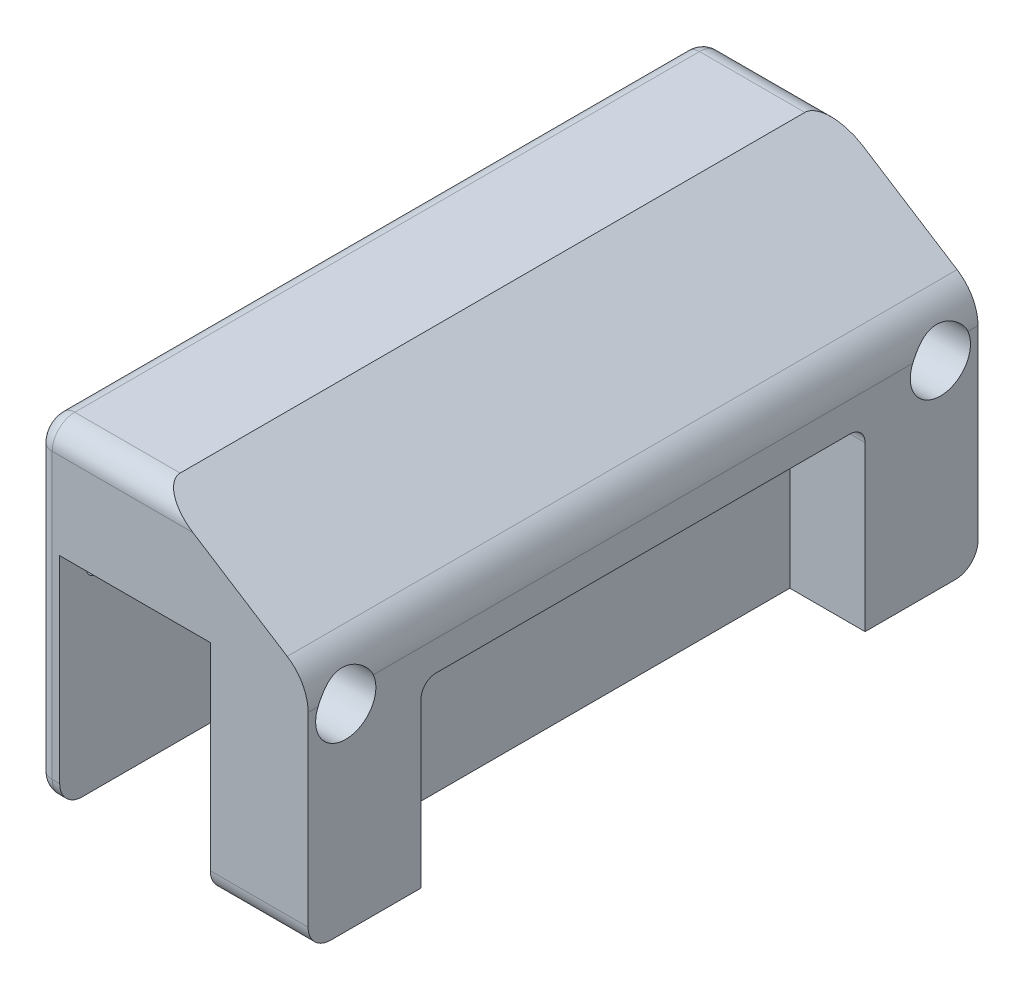
SolidWorks part; units mm, degrees
material "ABS"
ref_plane "Plano frontal" through (0, 0, 0) normal (0, 0, 1) x (1, 0, 0)
ref_plane "Plano superior" through (0, 0, 0) normal (0, 1, 0) x (1, 0, 0)
ref_plane "Plano direito" through (0, 0, 0) normal (1, 0, 0) x (0, 0, -1)
sketch "Esboço2" plane through (0, 0, 0) normal (1, 0, 0) x (0, 0, -1)
  line L1 (2.9016, -0.0625) -> (-35.0984, -0.0625) construction
  line L2 (2.9016, -0.0625) -> (-35.0984, -0.0625)
  line L6 (7.6893, -0.0625) -> (2.9016, -0.0625)
  line L8 (-39.8861, -0.0625) -> (-35.0984, -0.0625)
  line L9 (-60.5984, 9.4769) -> (-60.5984, 20.9769)
  line L10 (28.4016, 9.4769) -> (28.4016, 20.9769)
  line L11 (-57.5984, 23.9769) -> (25.4016, 23.9769)
  arc A0 (28.4016, 20.9769) -> (25.4016, 23.9769) centre (25.4016, 20.9769) ccw
  arc A1 (-60.5984, 20.9769) -> (-57.5984, 23.9769) centre (-57.5984, 20.9769) cw
  arc A2 (28.4016, 9.4769) -> (24.5016, 12.3387) centre (25.4016, 9.4769) ccw
  arc A3 (-48.8914, 5.5897) -> (-56.6984, 12.3387) centre (-60.5984, -0.0625) ccw
  arc A4 (-48.8914, 5.5897) -> (-39.8861, -0.0625) centre (-39.8861, 9.9375) ccw
  arc A5 (-60.5984, 9.4769) -> (-56.6984, 12.3387) centre (-57.5984, 9.4769) cw
  arc A6 (16.6946, 5.5897) -> (7.6893, -0.0625) centre (7.6893, 9.9375) cw
  arc A7 (16.6946, 5.5897) -> (24.5016, 12.3387) centre (28.4016, -0.0625) cw
  point P22 (28.4016, 12.9375)
  point P23 (-60.5984, 12.9375)
  dimension "D1" = 3
extrude "Ressalto-extrusão2" add sketch "Esboço2" along normal blind 30
sketch "Esboço3" plane through (0, 0, 0) normal (-1, 0, 0) x (0, 0, 1)
  line L0 (60.5984, 15.2269) -> (60.5984, 20.9769)
  line L1 (60.5984, 20.9769) -> (60.5984, 9.4769) construction
  line L2 (-28.4016, 15.2269) -> (-28.4016, 20.9769)
  line L3 (-28.4016, 9.4769) -> (-28.4016, 20.9769) construction
  line L4 (16.0984, 23.9769) -> (57.5984, 23.9769)
  line L5 (-25.4016, 23.9769) -> (57.5984, 23.9769) construction
  line L6 (16.0984, 23.9769) -> (-25.4016, 23.9769)
  line L7 (60.5984, 15.2269) -> (60.5984, -16.7731)
  line L8 (-28.4016, 15.2269) -> (-28.4016, -16.7731)
  line L9 (57.5984, -19.7731) -> (-25.4016, -19.7731)
  arc A0 (57.5984, 23.9769) -> (60.5984, 20.9769) centre (57.5984, 20.9769) cw
  arc A1 (-28.4016, 20.9769) -> (-25.4016, 23.9769) centre (-25.4016, 20.9769) cw
  arc A2 (-28.4016, -16.7731) -> (-25.4016, -19.7731) centre (-25.4016, -16.7731) ccw
  arc A3 (60.5984, -16.7731) -> (57.5984, -19.7731) centre (57.5984, -16.7731) cw
  dimension "D1" = 3
  dimension "D2" = 3
extrude "Ressalto-extrusão3" add sketch "Esboço3" along normal blind 3
sketch "Esboço4" plane through (30, 0, 0) normal (1, 0, 0) x (0, 0, -1)
  line L0 (-16.0984, 23.9769) -> (25.4016, 23.9769)
  line L1 (25.4016, 23.9769) -> (-57.5984, 23.9769) construction
  line L2 (-16.0984, 23.9769) -> (-57.5984, 23.9769)
  line L3 (28.4016, 15.2269) -> (28.4016, 20.9769)
  line L4 (28.4016, 9.4769) -> (28.4016, 20.9769) construction
  line L5 (-60.5984, 20.9769) -> (-60.5984, 15.2269)
  line L7 (28.4016, 15.2269) -> (28.4016, -16.7731)
  line L8 (28.4016, 9.4769) -> (28.4016, -16.7731) construction
  line L9 (-60.5984, 20.9769) -> (-60.5984, 9.4769) construction
  line L10 (-60.5984, 15.2269) -> (-60.5984, -16.7731)
  line L11 (25.4016, -19.7731) -> (-57.5984, -19.7731)
  arc A0 (25.4016, 23.9769) -> (28.4016, 20.9769) centre (25.4016, 20.9769) cw
  arc A1 (-60.5984, 20.9769) -> (-57.5984, 23.9769) centre (-57.5984, 20.9769) cw
  arc A2 (-60.5984, -16.7731) -> (-57.5984, -19.7731) centre (-57.5984, -16.7731) ccw
  arc A3 (28.4016, -16.7731) -> (25.4016, -19.7731) centre (25.4016, -16.7731) cw
  point P23 (28.4016, -19.7731)
  dimension "D1" = 3
extrude "Ressalto-extrusão4" add sketch "Esboço4" along normal blind 3 and the other way blind 10
sketch "Esboço8" plane through (33, 0, 0) normal (1, 0, 0) x (0, 0, -1)
  line L0 (-60.5984, 20.9769) -> (-60.5984, -16.7731) construction
  line L1 (-43.5984, 3.9769) -> (11.4016, 3.9769)
  line L2 (-45.5984, 1.9769) -> (-45.5984, -7.7731)
  line L4 (13.4016, 1.9769) -> (13.4016, -7.7731)
  line L5 (28.4016, -16.7731) -> (28.4016, 20.9769) construction
  line L6 (25.4016, 23.9769) -> (-57.5984, 23.9769) construction
  line L7 (-57.5984, -19.7731) -> (25.4016, -19.7731) construction
  line L9 (-45.5984, -7.7731) -> (-45.5984, -19.7731)
  line L10 (-45.5984, -19.7731) -> (13.4016, -19.7731)
  line L11 (13.4016, -7.7731) -> (13.4016, -19.7731)
  arc A0 (-43.5984, 3.9769) -> (-45.5984, 1.9769) centre (-43.5984, 1.9769) ccw
  arc A2 (11.4016, 3.9769) -> (13.4016, 1.9769) centre (11.4016, 1.9769) cw
  point P1 (0, 0)
  point P2 (0, 0)
  point P10 (0, 0)
  point P11 (13.4016, -19.7731)
  point P12 (-45.5984, -19.7731)
  point P13 (0, 0)
  point P19 (13.8268, -19.7731)
  point P22 (13.4016, 3.9769)
  point P23 (-45.5984, -19.4909)
  point P28 (13.4016, -9.7731)
  point P31 (13.4016, -19.7731)
  dimension "D9" = 2
  dimension "D10" = 0
  dimension "D1" = 15
  dimension "D2" = 15
  dimension "D3" = 20
  dimension "D4" = 0
  dimension "D5" = 15
  dimension "D6" = 15
  dimension "D7" = 0
  dimension "D8" = 10
extrude "Corte-extrusão1" cut sketch "Esboço8" against normal blind 10
sketch "Esboço9" plane through (0, -19.7731, 0) normal (0, -1, 0) x (-1, 0, 0)
  line L0 (-20, 28.4016) -> (-33, 28.4016) construction
  line L1 (-25, 13.4016) -> (-28, 13.4016)
  line L2 (-23, 11.4016) -> (-23, -43.5984)
  line L3 (-25, -45.5984) -> (-28, -45.5984)
  line L4 (-30, 11.4016) -> (-30, -43.5984)
  line L5 (-20, -60.5984) -> (-33, -60.5984) construction
  line L6 (-33, -57.5984) -> (-33, -45.5984) construction
  line L7 (-20, -57.5984) -> (-20, 25.4016) construction
  arc A0 (-28, -45.5984) -> (-30, -43.5984) centre (-28, -43.5984) cw
  arc A1 (-23, -43.5984) -> (-25, -45.5984) centre (-25, -43.5984) cw
  arc A2 (-28, 13.4016) -> (-30, 11.4016) centre (-28, 11.4016) ccw
  arc A3 (-25, 13.4016) -> (-23, 11.4016) centre (-25, 11.4016) cw
  dimension "D5" = 2
  dimension "D1" = 15
  dimension "D2" = 15
  dimension "D3" = 3
  dimension "D4" = 3
extrude "Corte-extrusão2" cut sketch "Esboço9" against normal up to surface (23.75 mm away) up to face at (28, 3.9769, 16.0984)
sketch "Esboço10" plane through (0, 0, 0) normal (1, 0, 0) x (0, 0, -1)
  line L0 (-60.5984, -16.7731) -> (-60.5984, 9.4769) construction
  line L1 (28.4016, 9.4769) -> (28.4016, -16.7731) construction
  line L2 (-39.8861, -0.0625) -> (7.6893, -0.0625) construction
  circle A0 centre (-55.5984, 6.3387) radius 1.5
  circle A1 centre (23.4016, 6.3387) radius 1.5
  circle A2 centre (-16.0984, -8.5625) radius 1.5
  dimension "D1" = 3
  dimension "D2" = 3
  dimension "D3" = 3
  dimension "D4" = 5
  dimension "D5" = 6
  dimension "D6" = 5
  dimension "D7" = 6
  dimension "D8" = 8.5
  dimension "D9" = 44.5
extrude "Corte-extrusão3" cut sketch "Esboço10" against normal blind 10
sketch "Esboço12" plane through (0, 0, 0) normal (1, 0, 0) x (0, 0, -1)
  line L0 (28.4016, 9.4769) -> (28.4016, -16.7731) construction
  line L1 (-31.5984, -2.8625) -> (-25.5984, -2.8625)
  line L2 (-33.5984, -4.8625) -> (-33.5984, -14.7731)
  line L3 (-31.5984, -16.7731) -> (-25.5984, -16.7731)
  line L4 (-23.5984, -4.8625) -> (-23.5984, -14.7731)
  line L5 (-6.5984, -2.8625) -> (-0.5984, -2.8625)
  line L6 (-8.5984, -4.8625) -> (-8.5984, -14.7731)
  line L7 (-6.5984, -16.7731) -> (-0.5984, -16.7731)
  line L8 (1.4016, -4.8625) -> (1.4016, -14.7731)
  line L9 (-60.5984, -16.7731) -> (-60.5984, 9.4769) construction
  line L10 (25.4016, -19.7731) -> (-57.5984, -19.7731) construction
  line L11 (-39.8861, -0.0625) -> (7.6893, -0.0625) construction
  arc A0 (-0.5984, -2.8625) -> (1.4016, -4.8625) centre (-0.5984, -4.8625) cw
  arc A1 (-0.5984, -16.7731) -> (1.4016, -14.7731) centre (-0.5984, -14.7731) ccw
  arc A2 (-8.5984, -14.7731) -> (-6.5984, -16.7731) centre (-6.5984, -14.7731) ccw
  arc A3 (-6.5984, -2.8625) -> (-8.5984, -4.8625) centre (-6.5984, -4.8625) ccw
  arc A4 (-25.5984, -2.8625) -> (-23.5984, -4.8625) centre (-25.5984, -4.8625) cw
  arc A5 (-25.5984, -16.7731) -> (-23.5984, -14.7731) centre (-25.5984, -14.7731) ccw
  arc A6 (-31.5984, -2.8625) -> (-33.5984, -4.8625) centre (-31.5984, -4.8625) ccw
  arc A7 (-33.5984, -14.7731) -> (-31.5984, -16.7731) centre (-31.5984, -14.7731) ccw
  point P12 (-60.5984, -3.6481)
  point P21 (1.4016, -16.7731)
  point P24 (-8.5984, -16.7731)
  point P31 (-23.5984, -16.7731)
  point P36 (-33.5984, -16.7731)
  dimension "D9" = 2
  dimension "D1" = 52
  dimension "D2" = 52
  dimension "D3" = 3
  dimension "D4" = 3
  dimension "D5" = 2.8
  dimension "D6" = 2.8
  dimension "D7" = 10
  dimension "D8" = 10
extrude "Corte-extrusão4" cut sketch "Esboço12" against normal blind 10
fillet "Filete2" radius 2 8 edges at (-3, 23.0982, 59.7197) (-3, 2.1019, 60.5984) (-3, -18.8944, 59.7197) (-3, -19.7731, 16.0984) (-3, -18.8944, -27.5229) (-3, 2.1019, -28.4016) (-3, 23.0982, -27.5229) (-3, 23.9769, 16.0984)
sketch "Esboço13" plane through (-3, 0, 0) normal (-1, 0, 0) x (0, 0, 1)
  line L0 (57.5984, 21.9769) -> (-25.4016, 21.9769) construction
  line L2 (-26.4016, 20.9769) -> (-26.4016, -16.7731) construction
  circle A0 centre (27.4484, 3.9769) radius 1.5
  circle A1 centre (4.7484, 3.9769) radius 1.5
  point P10 (-26.4016, 2.1019)
  dimension "D1" = 22.7
  dimension "D2" = 3
  dimension "D3" = 3
  dimension "D4" = 18
  dimension "D5" = 31.15
extrude "Corte-extrusão5" cut sketch "Esboço13" against normal blind 16
ref_plane "Plano1" through (0, 0, -38.4016) normal (0, 0, -1) x (-1, 0, 0)
sketch "Esboço16" plane through (0, 0, -38.4016) normal (0, 0, -1) x (-1, 0, 0)
  line L0 (-13, 23.9769) -> (-33, 11.2262)
  line L1 (-33, 23.9769) -> (-13, 23.9769)
  line L2 (-33, 23.9769) -> (-33, 11.2262)
  point P1 (-13.9874, 23.9769)
  point P5 (-33, 11.2262)
  point P6 (-10.0045, 23.9769)
  dimension "D1" = 20
extrude "Corte-extrusão11" cut sketch "Esboço16" against normal blind 117 contours L0 L2 L1
fillet "Filete7" radius 6 1 edges at (33, 11.2262, 16.0984)
sketch "Esboço18" plane through (20, 0, 0) normal (-1, 0, 0) x (0, 0, 1)
  circle A0 centre (-23.4016, 6.3387) radius 4
  dimension "D1" = 8
extrude "Corte-extrusão13" cut sketch "Esboço18" against normal blind 22
sketch "Esboço19" plane through (20, 0, 0) normal (-1, 0, 0) x (0, 0, 1)
  circle A0 centre (55.5984, 6.3387) radius 4
  dimension "D1" = 8
extrude "Corte-extrusão14" cut sketch "Esboço19" against normal blind 22 contours A0
